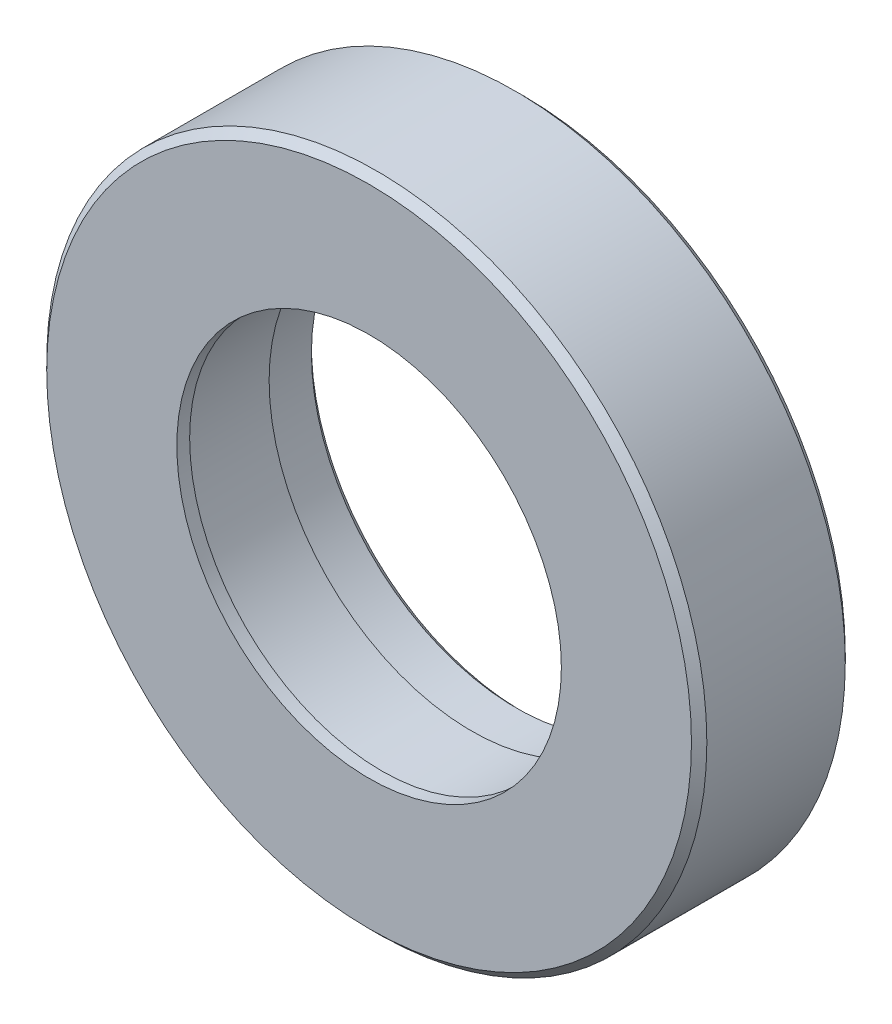
SolidWorks part; units mm, degrees
ref_plane "Front Plane" through (0, 0, 0) normal (0, 0, 1) x (1, 0, 0)
ref_plane "Top Plane" through (0, 0, 0) normal (0, 1, 0) x (1, 0, 0)
ref_plane "Right Plane" through (0, 0, 0) normal (1, 0, 0) x (0, 0, -1)
sketch "Sketch1" plane through (0, 0, 0) normal (0, 0, 1) x (1, 0, 0)
  circle A0 centre (0, 0) radius 25.75
  dimension "D1" = 51.5
extrude "Boss-Extrude1" add sketch "Sketch1" along normal blind 12
chamfer "Chamfer1" distance 0.6 angle 45 2 edges at (25.75, 0, 0) (25.75, 0, 12)
sketch "Sketch2" plane through (0, 0, 12) normal (0, 0, 1) x (1, 0, 0)
  circle A0 centre (0, 0) radius 15
extrude "Cut-Extrude1" cut sketch "Sketch2" against normal through all
sketch "Sketch3" plane through (0, 0, 0) normal (0, 0, -1) x (-1, 0, 0)
  circle A0 centre (0, 0) radius 15.8
  dimension "D1" = 31.6
extrude "Cut-Extrude2" cut sketch "Sketch3" against normal blind 11
sketch "Sketch4" plane through (0, 0, 0) normal (0, 0, -1) x (-1, 0, 0)
  circle A0 centre (0, 0) radius 16
  dimension "D1" = 32
extrude "Cut-Extrude3" cut sketch "Sketch4" against normal blind 4
chamfer "Chamfer2" distance 0.5 angle 45 1 edges at (-16, 0, 0)
